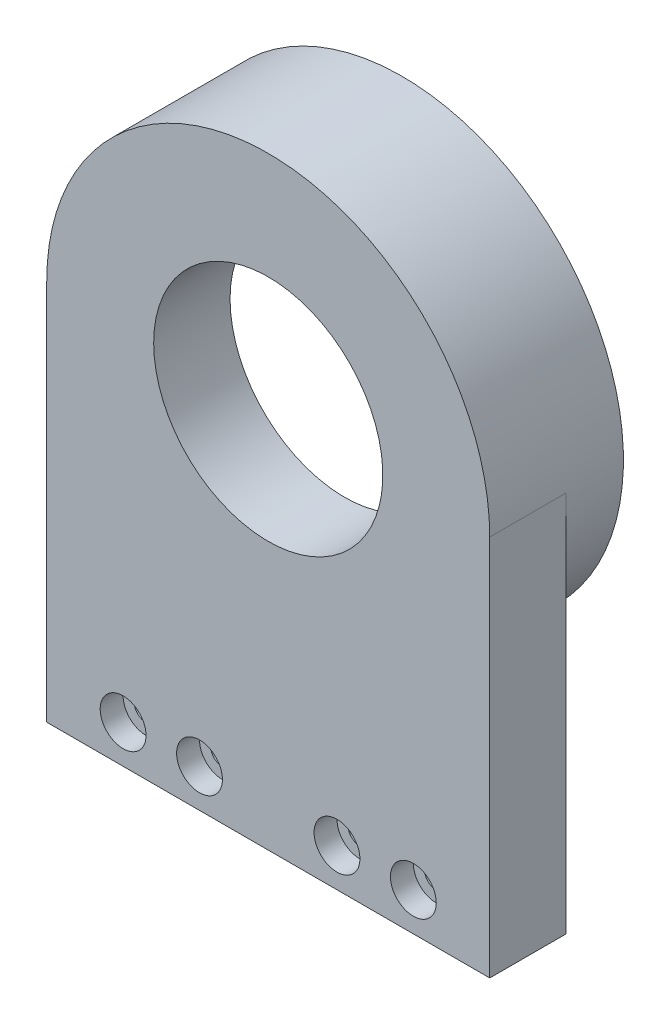
SolidWorks part; units mm, degrees
ref_plane "前视基准面" through (0, 0, 0) normal (0, 0, 1) x (1, 0, 0)
ref_plane "上视基准面" through (0, 0, 0) normal (0, 1, 0) x (1, 0, 0)
ref_plane "右视基准面" through (0, 0, 0) normal (1, 0, 0) x (0, 0, -1)
sketch "草图1" plane through (0, 0, 0) normal (0, 0, 1) x (1, 0, 0)
  line L1 (-29, 25) -> (29, 25)
  line L2 (-29, 25) -> (-29, -25)
  line L3 (-29, -25) -> (29, -25)
  line L4 (29, 25) -> (29, -25)
  line L5 (0, -25) -> (0, 25) construction
  line L6 (-29, 0) -> (29, 0) construction
  arc A0 (-29, 25) -> (29, 25) centre (0, 25) cw
  point P0 (0, 0)
  dimension "D1" = 58
  dimension "D2" = 50
extrude "凸台-拉伸1" add sketch "草图1" along normal blind 10 contours A0 L1 | L4 L1 L2 L3
sketch "草图2" plane through (0, 0, 0) normal (0, 0, -1) x (-1, 0, 0)
  circle A0 centre (0, 25) radius 29
  circle A1 centre (0, 25) radius 26.1
  dimension "D1" = 58
  dimension "D2" = 52.2
extrude "凸台-拉伸2" add sketch "草图2" along normal blind 7.5
sketch "草图3" plane through (0, 0, 0) normal (0, 0, -1) x (-1, 0, 0)
  circle A0 centre (0, 25) radius 24
  circle A2 centre (0, 25) radius 26.1 construction
  circle A3 centre (0, 25) radius 26.1
  dimension "D1" = 48
extrude "凸台-拉伸3" add sketch "草图3" along normal blind 0.5
sketch "草图4" plane through (0, 0, 0) normal (0, 0, -1) x (-1, 0, 0)
  line L0 (0, -1.1) -> (0, -28.635) construction
  line L1 (-35.748, -20) -> (39.5283, -20) construction
  line L2 (29, -25) -> (-29, -25) construction
  line L3 (-29, 25) -> (-29, -25) construction
  line L4 (29, 25) -> (29, -25) construction
  line L5 (-29, -15) -> (-23, -15)
  line L6 (-29, -20) -> (-23, -20)
  line L7 (-29, -20) -> (-29, -25)
  line L8 (-29, -25) -> (-23, -25)
  line L9 (-23, -20) -> (-23, -25)
  line L10 (-23, -20) -> (-23, -15)
  line L11 (-29, -20) -> (-23, -20)
  line L12 (-29, -20) -> (-29, -15)
  line L13 (29, -25) -> (23, -25)
  line L14 (23, -20) -> (23, -25)
  line L15 (29, -20) -> (23, -20)
  line L16 (29, -20) -> (29, -25)
  line L17 (29, -20) -> (29, -15)
  line L18 (29, -20) -> (23, -20)
  line L19 (23, -20) -> (23, -15)
  line L20 (29, -15) -> (23, -15)
  circle A0 centre (0, 25) radius 26.1 construction
  circle A1 centre (0, 25) radius 26.1 construction
  line M2 (-29, 25) -> (-29, -25)
  line M3 (-29, -25) -> (29, -25)
  line M4 (29, -25) -> (29, 25)
  dimension "D1" = 5
  dimension "D2" = 5
  dimension "D3" = 6
extrude "凸台-拉伸4" [suppressed] add sketch "草图4" along normal blind 8 contours L6 L10 L5 M2 | L9 L6 M2 M3 | L20 L19 L15 M4 | L15 L14 M4 M3
sketch "草图5" plane through (0, 0, 0) normal (0, 0, -1) x (-1, 0, 0)
  line L0 (-35.748, -20) -> (39.5283, -20) construction
  line L1 (0, -1.1) -> (0, -28.635) construction
  line L2 (0, -1.1) -> (0, -28.635) construction
  circle A0 centre (-19, -20) radius 1.55
  circle A1 centre (-9, -20) radius 1.55
  circle A2 centre (9, -20) radius 1.55
  circle A3 centre (19, -20) radius 1.55
  dimension "D1" = 3.1
  dimension "D2" = 3.1
  dimension "D3" = 10
  dimension "D4" = 10
extrude "切除-拉伸1" cut sketch "草图5" against normal up to next
sketch "草图6" plane through (0, 0, 10) normal (0, 0, 1) x (1, 0, 0)
  circle A0 centre (19, -20) radius 3
  circle A1 centre (9, -20) radius 3
  circle A2 centre (-9, -20) radius 3
  circle A3 centre (-19, -20) radius 3
  dimension "D1" = 6
extrude "切除-拉伸2" cut sketch "草图6" against normal blind 3
sketch "草图7" plane through (0, 0, 0) normal (0, 0, -1) x (-1, 0, 0)
  circle A0 centre (0, 25) radius 15
  dimension "D1" = 30
extrude "切除-拉伸3" cut sketch "草图7" against normal through all
